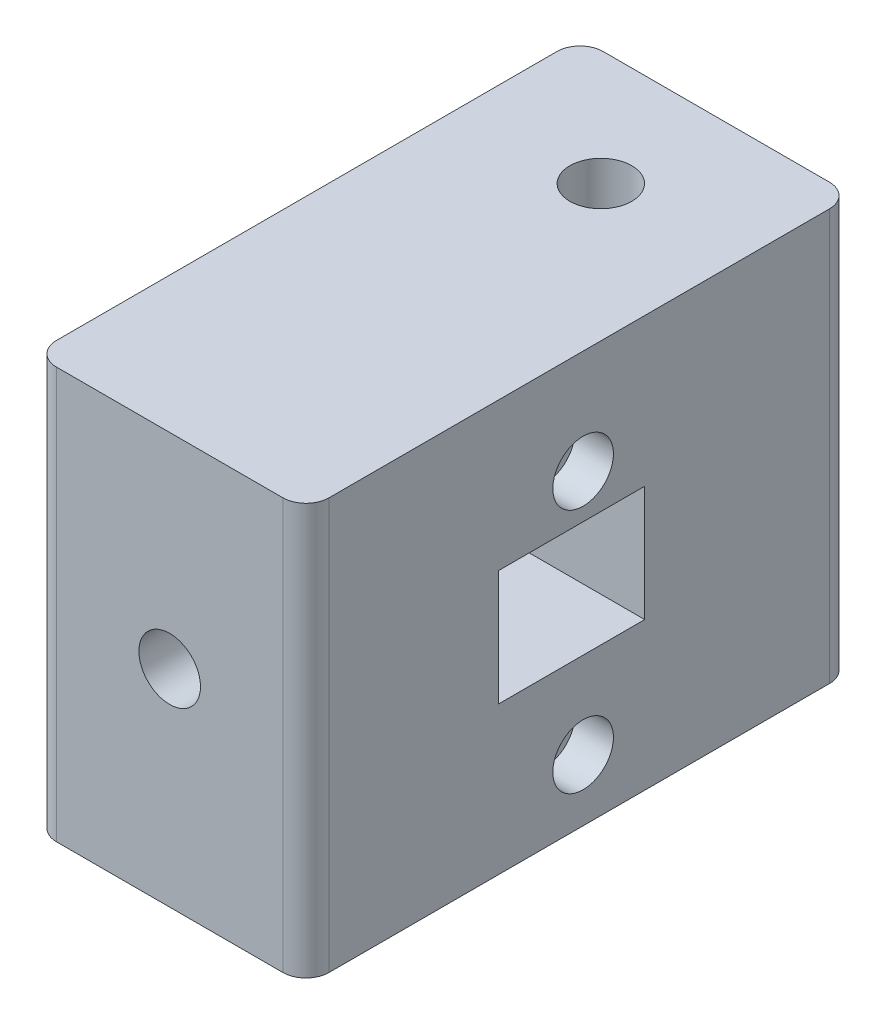
SolidWorks part; units mm, degrees
ref_plane "Front Plane" through (0, 0, 0) normal (0, 0, 1) x (1, 0, 0)
ref_plane "Top Plane" through (0, 0, 0) normal (0, 1, 0) x (1, 0, 0)
ref_plane "Right Plane" through (0, 0, 0) normal (1, 0, 0) x (0, 0, -1)
sketch "Sketch1" plane through (0, 0, 0) normal (0, 0, 1) x (1, 0, 0)
  line L1 (0, 0) -> (44.958, 0)
  line L2 (0, 0) -> (0, 67.818)
  line L3 (0, 67.818) -> (44.958, 67.818)
  line L4 (44.958, 0) -> (44.958, 67.818)
  dimension "D1" = 44.958
  dimension "D2" = 67.818
extrude "Boss-Extrude1" add sketch "Sketch1" along normal blind 90.17
sketch "Sketch2" plane through (44.958, 0, 0) normal (1, 0, 0) x (0, 0, -1)
  line L0 (-90.17, 0) -> (-90.17, 67.818) construction
  line L1 (-44.45, 50.66) -> (-44.45, 10.16) construction
  line L2 (-90.17, 0) -> (0, 0) construction
  circle A0 centre (-44.45, 50.66) radius 5
  circle A1 centre (-44.45, 10.16) radius 5
  dimension "D2" = 10
  dimension "D4" = 10
  dimension "D1" = 45.72
  dimension "D3" = 40.5
  dimension "D5" = 10.16
extrude "Cut-Extrude1" cut sketch "Sketch2" against normal blind 6.35
sketch "Sketch3" plane through (0, 67.818, 0) normal (0, 1, 0) x (1, 0, 0)
  line L0 (44.958, 0) -> (0, 0) construction
  line L1 (0, -90.17) -> (0, 0) construction
  circle A0 centre (22.479, -19.05) radius 4.064
  dimension "D1" = 8.128
  dimension "D2" = 19.05
  dimension "D3" = 22.479
extrude "Cut-Extrude2" cut sketch "Sketch3" against normal through all
sketch "Sketch4" plane through (0, 67.818, 0) normal (0, 1, 0) x (1, 0, 0)
  circle A0 centre (22.479, -19.05) radius 5.1
  dimension "D1" = 10.2
extrude "Cut-Extrude3" cut sketch "Sketch4" against normal blind 15.24
sketch "Sketch5" plane through (0, 0, 90.17) normal (0, 0, 1) x (1, 0, 0)
  line L0 (0, 0) -> (44.958, 0) construction
  line L1 (0, 67.818) -> (0, 0) construction
  circle A0 centre (22.479, 34.036) radius 5.08
  dimension "D3" = 10.16
  dimension "D1" = 34.036
  dimension "D2" = 22.479
extrude "Cut-Extrude4" cut sketch "Sketch5" against normal blind 50.8
sketch "Sketch6" plane through (44.958, 0, 0) normal (1, 0, 0) x (0, 0, -1)
  line L0 (-90.17, 0) -> (0, 0) construction
  line L1 (-58.42, 43.434) -> (-34.29, 43.434)
  line L2 (-58.42, 43.434) -> (-58.42, 24.384)
  line L3 (-58.42, 24.384) -> (-34.29, 24.384)
  line L4 (-34.29, 43.434) -> (-34.29, 24.384)
  line L5 (-90.17, 0) -> (-90.17, 67.818) construction
  dimension "D1" = 24.13
  dimension "D2" = 19.05
  dimension "D3" = 24.384
  dimension "D4" = 55.88
extrude "Cut-Extrude5" cut sketch "Sketch6" against normal blind 34.29
fillet "Fillet1" radius 3.81 4 edges at (0, 33.909, 0) (44.958, 33.909, 0) (0, 33.909, 90.17) (44.958, 33.909, 90.17)
